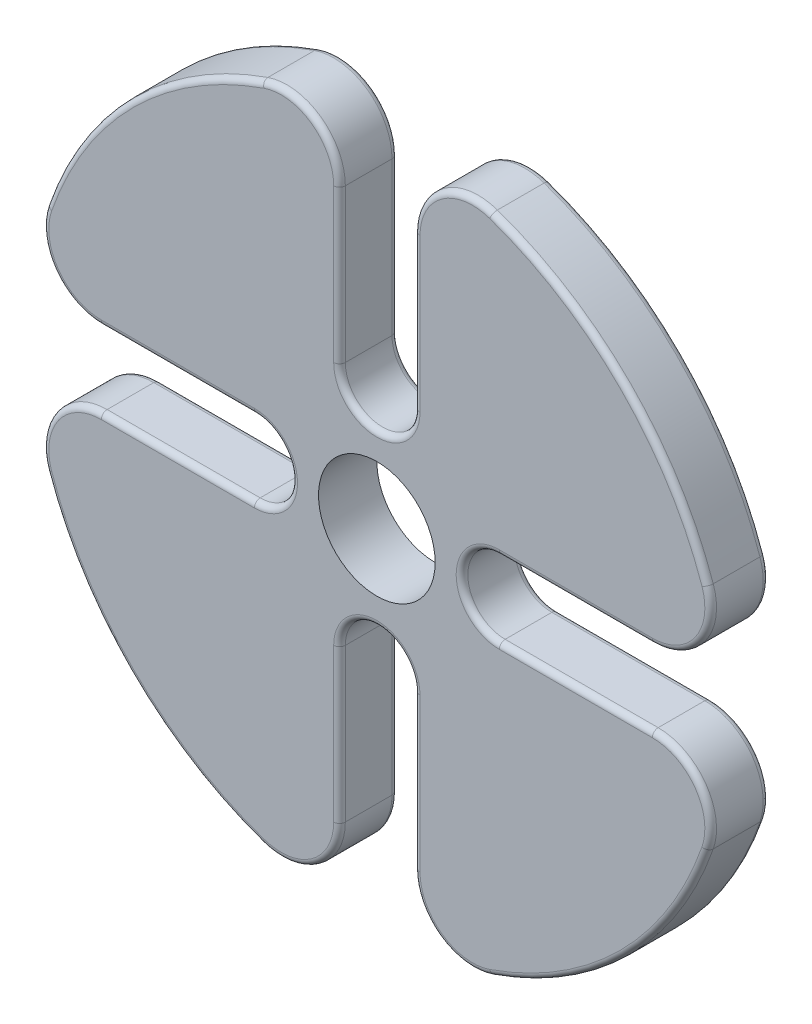
SolidWorks part; units mm, degrees
ref_plane "Přední rovina" through (0, 0, 0) normal (0, 0, 1) x (1, 0, 0)
ref_plane "Vrchní rovina" through (0, 0, 0) normal (0, 1, 0) x (1, 0, 0)
ref_plane "Pravá rovina" through (0, 0, 0) normal (1, 0, 0) x (0, 0, -1)
sketch "Skica1" plane through (0, 0, 0) normal (0, 0, 1) x (1, 0, 0)
  line L0 (0, 55.6712) -> (0, -37.6542) construction
  line L1 (95.7882, 0) -> (-55.9953, 0) construction
  line L2 (-3.2, 29.8288) -> (-3.2, 10.5)
  line L3 (3.2, 10.5) -> (3.2, 29.8288)
  line L4 (29.8288, 3.2) -> (10.5, 3.2)
  line L5 (10.5, -3.2) -> (29.8288, -3.2)
  line L6 (3.2, -29.8288) -> (3.2, -10.5)
  line L7 (-3.2, -10.5) -> (-3.2, -29.8288)
  line L8 (-29.8288, -3.2) -> (-10.5, -3.2)
  line L9 (-10.5, 3.2) -> (-29.8288, 3.2)
  arc A0 (-3.2, 29.8288) -> (-29.8288, 3.2) centre (0, 0) ccw
  circle A1 centre (0, 0) radius 5
  arc A2 (-3.2, 10.5) -> (3.2, 10.5) centre (0, 10.5) ccw
  arc A3 (10.5, 3.2) -> (10.5, -3.2) centre (10.5, 0) ccw
  arc A4 (3.2, -10.5) -> (-3.2, -10.5) centre (0, -10.5) ccw
  arc A5 (-10.5, -3.2) -> (-10.5, 3.2) centre (-10.5, 0) ccw
  arc A6 (-29.8288, -3.2) -> (-3.2, -29.8288) centre (0, 0) ccw
  arc A7 (3.2, -29.8288) -> (29.8288, -3.2) centre (0, 0) ccw
  arc A8 (29.8288, 3.2) -> (3.2, 29.8288) centre (0, 0) ccw
  point P6 (0, 0)
  point P30 (0, 0)
  dimension "D1" = 60
  dimension "D2" = 10
  dimension "D4" = 10.5
  dimension "D3" = 6.4
  dimension "D5" = 4
extrude "Přidat vysunutím1" add sketch "Skica1" along normal blind 5
fillet "Zaoblit1" radius 5 8 edges at (-3.2, 29.8288, 2.5) (3.2, 29.8288, 2.5) (29.8288, 3.2, 2.5) (29.8288, -3.2, 2.5) (3.2, -29.8288, 2.5) (-3.2, -29.8288, 2.5) (-29.8288, -3.2, 2.5) (-29.8288, 3.2, 2.5)
fillet "Zaoblit2" radius 0.5 48 edges at (-27.6913, 5.3017, 0) (-17.0585, 3.2, 0) (-7.3, 0, 0) (-17.0585, -3.2, 0) (-27.6913, -5.3017, 0) (-21.2132, -21.2132, 0) (-5.3017, -27.6913, 0) (-3.2, -17.0585, 0) (0, -7.3, 0) (3.2, -17.0585, 0) (5.3017, -27.6913, 0) (21.2132, -21.2132, 0) (27.6913, -5.3017, 0) (17.0585, -3.2, 0) (7.3, 0, 0) (17.0585, 3.2, 0) (27.6913, 5.3017, 0) (21.2132, 21.2132, 0) (5.3017, 27.6913, 0) (3.2, 17.0585, 0) (0, 7.3, 0) (-3.2, 17.0585, 0) (-5.3017, 27.6913, 0) (-21.2132, 21.2132, 0) (0, 7.3, 5) (3.2, 17.0585, 5) (5.3017, 27.6913, 5) (21.2132, 21.2132, 5) (27.6913, 5.3017, 5) (17.0585, 3.2, 5) (7.3, 0, 5) (17.0585, -3.2, 5) (27.6913, -5.3017, 5) (21.2132, -21.2132, 5) (5.3017, -27.6913, 5) (3.2, -17.0585, 5) (0, -7.3, 5) (-3.2, -17.0585, 5) (-5.3017, -27.6913, 5) (-21.2132, -21.2132, 5) (-27.6913, -5.3017, 5) (-17.0585, -3.2, 5) (-7.3, 0, 5) (-17.0585, 3.2, 5) (-27.6913, 5.3017, 5) (-21.2132, 21.2132, 5) (-5.3017, 27.6913, 5) (-3.2, 17.0585, 5)
